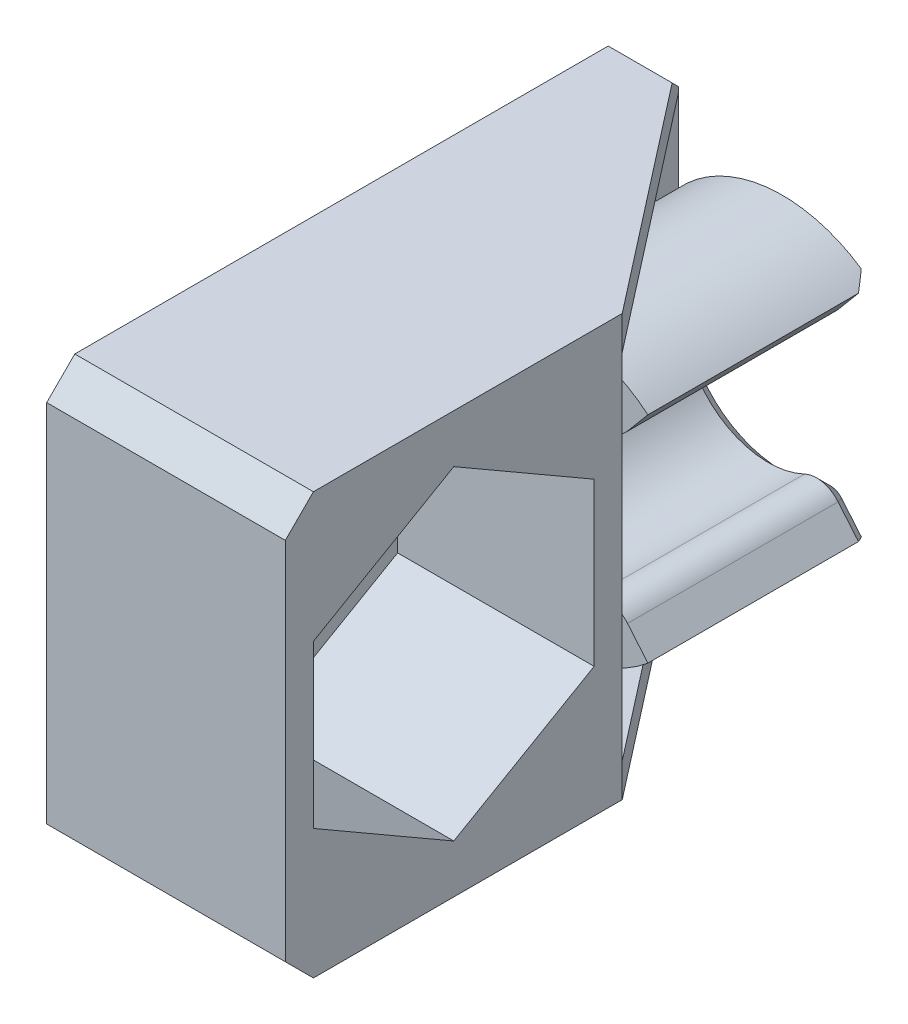
SolidWorks part; units mm, degrees
ref_plane "Alzado" through (0, 0, 0) normal (0, 0, 1) x (1, 0, 0)
ref_plane "Planta" through (0, 0, 0) normal (0, 1, 0) x (1, 0, 0)
ref_plane "Vista lateral" through (0, 0, 0) normal (1, 0, 0) x (0, 0, -1)
sketch "Croquis1" plane through (0, 0, 0) normal (0, 0, 1) x (1, 0, 0)
  line L0 (0, 0) -> (9856.1717, 0) construction
  line L1 (0, 0) -> (0, 9856.1717) construction
  line L2 (4, -13.8382) -> (4, 9842.3335) construction
  line L3 (10, -15.0775) -> (10, 9841.0942) construction
  line L4 (-4, -13.8382) -> (-4, 9842.3335) construction
  line L5 (-10, -15.0775) -> (-10, 9841.0942) construction
  line L6 (-5.2, 1.704) -> (-5.2, 50001.704) construction
  line L7 (-8.2, -11.9793) -> (-8.2, 49988.0207) construction
  line L8 (-26.2702, -15) -> (49973.7298, -15) construction
  line L9 (0, 0) -> (7.8369, 9.3397) construction
  line L10 (1.9284, 2.2981) -> (3.2139, 3.8302)
  line L11 (0, 0) -> (6.4279, -7.6604) construction
  line L13 (1.9284, -2.2981) -> (3.2139, -3.8302)
  line L14 (-4.3301, 2.5) -> (-5.2, 2.5)
  line L15 (-5.2, 2.5) -> (-5.2, -2.5)
  line L16 (-5.2, -2.5) -> (-4.3301, -2.5)
  circle A0 centre (0, 0) radius 3 construction
  arc A1 (1.9284, 2.2981) -> (1.9284, -2.2981) centre (0, 0) ccw
  arc A2 (3.2139, 3.8302) -> (-4.3301, 2.5) centre (0, 0) ccw
  arc A4 (-4.3301, -2.5) -> (3.2139, -3.8302) centre (0, 0) ccw
  point P29 (-5.2, 0)
  dimension "D3" = 6
  dimension "D6" = 15
  dimension "D7" = 50
  dimension "D8" = 2
  dimension "D9" = 5
  dimension "D1" = 4
  dimension "D2" = 10
  dimension "D4" = 1.2
  dimension "D5" = 3
extrude "Saliente-Extruir1" add sketch "Croquis1" along normal blind 8
sketch "Croquis3" plane through (-5.2, 0, 0) normal (-1, 0, 0) x (0, 0, 1)
  line L0 (0, 0) -> (0, 49942.1244) construction
  line L1 (0, 7.5) -> (21, 7.5)
  line L2 (0, 7.5) -> (0, -7.5)
  line L3 (0, -7.5) -> (21, -7.5)
  line L4 (21, 7.5) -> (21, -7.5)
  line L5 (0, 7.5) -> (21, -7.5) construction
  line L6 (0, -7.5) -> (21, 7.5) construction
  line L7 (0, 0) -> (50000, 0) construction
  point P4 (10.5, 0)
  dimension "D1" = 21
  dimension "D2" = 15
extrude "Saliente-Extruir2" add sketch "Croquis3" against normal blind 1.5
sketch "Croquis4" plane through (-5.2, 0, 0) normal (-1, 0, 0) x (0, 0, 1)
  line L0 (0, 0) -> (50000, 0) construction
  circle A0 centre (15, 0) radius 3
  point P9 (0, 0)
  dimension "D1" = 6
  dimension "D2" = 15
extrude "Cortar-Extruir1" cut sketch "Croquis4" against normal through all
sketch "Croquis5" plane through (-3.7, 0, 0) normal (1, 0, 0) x (0, 0, -1)
  line L1 (-21, 7.5) -> (-9, 7.5)
  line L2 (-21, 7.5) -> (-21, -7.5)
  line L3 (-21, -7.5) -> (-9, -7.5)
  line L4 (-9, 7.5) -> (-9, -7.5)
  line L5 (-21, 7.5) -> (-9, -7.5) construction
  line L6 (-21, -7.5) -> (-9, 7.5) construction
  line L8 (0, 0) -> (-50000, 0) construction
  point P4 (-15, 0)
extrude "Saliente-Extruir3" add sketch "Croquis5" along normal blind 7
sketch "Croquis7" plane through (3.3, 0, 0) normal (1, 0, 0) x (0, 0, -1)
  line L1 (-10, -2.8868) -> (-10, 2.8868)
  line L2 (-10, 2.8868) -> (-15, 5.7735)
  line L3 (-15, 5.7735) -> (-20, 2.8868)
  line L4 (-20, 2.8868) -> (-20, -2.8868)
  line L5 (-20, -2.8868) -> (-15, -5.7735)
  line L6 (-15, -5.7735) -> (-10, -2.8868)
  circle A0 centre (-15, 0) radius 5 construction
  dimension "D1" = 10
extrude "Cortar-Extruir2" cut sketch "Croquis7" against normal up to surface (7 mm away) up to face at (-3.7, 0, 4.25)
fillet "Redondeo1" radius 1 2 edges at (1.9284, -2.2981, 4) (1.9284, 2.2981, 4)
chamfer "Chaflán1" distance 0.5 angle 45 5 edges at (2.8517, -3.3985, 0) (2.8517, 3.3985, 0) (1.9354, -2.6324, 0) (1.9354, 2.6324, 0) (-3, 0, 0)
sketch "Croquis8" plane through (0, 7.5, 0) normal (0, 1, 0) x (1, 0, 0)
  line L0 (-3.7, 0) -> (3.3, -9)
  line L1 (3.3, -9) -> (-3.7, -9)
  line L2 (-3.7, -9) -> (-3.7, 0)
extrude "Saliente-Extruir4" add sketch "Croquis8" against normal blind 1.2
mirror "Simetría1" about plane through (0, 0, 0) normal (0, 1, 0) of "Saliente-Extruir4"
chamfer "Chaflán2" distance 1 angle 45 4 edges at (-0.95, 7.5, 21) (-0.95, -7.5, 21) (-4.45, -7.5, 0) (-4.45, 7.5, 0)
